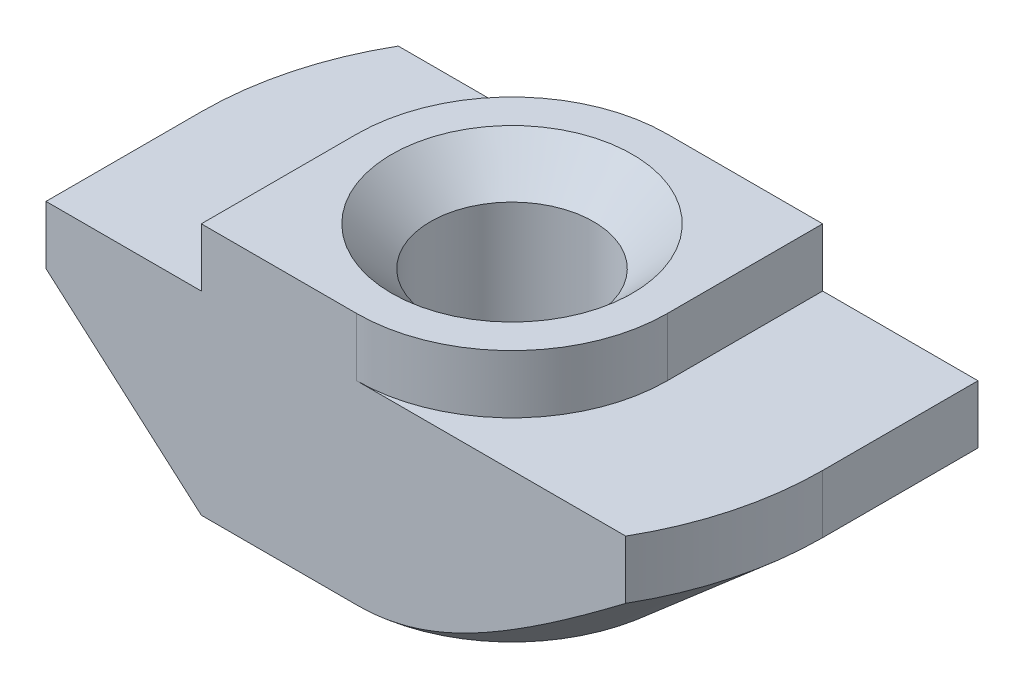
SolidWorks part; units mm, degrees
material "Сталь 20  ГОСТ 1050-2013"
ref_plane "Спереди" through (0, 0, 0) normal (0, 0, 1) x (1, 0, 0)
ref_plane "Сверху" through (0, 0, 0) normal (0, 1, 0) x (1, 0, 0)
ref_plane "Справа" through (0, 0, 0) normal (1, 0, 0) x (0, 0, -1)
sketch "Эскиз1" plane through (0, 0, 0) normal (0, 0, 1) x (1, 0, 0)
  line L0 (4, 0) -> (-4, 0)
  line L1 (-4, 0) -> (-4, -1.5)
  line L2 (-4, -1.5) -> (-8, -1.5)
  line L3 (-8, -1.5) -> (-8, -6.5)
  line L4 (-8, -6.5) -> (8, -6.5)
  line L5 (0, -6.5) -> (0, 0) construction
  line L6 (8, -1.5) -> (8, -6.5)
  line L7 (4, -1.5) -> (8, -1.5)
  line L8 (4, 0) -> (4, -1.5)
  dimension "D1" = 8
  dimension "D2" = 16
  dimension "D3" = 6.5
  dimension "D4" = 1.5
extrude "Бобышка-Вытянуть1" add sketch "Эскиз1" along normal mid plane 8
hole_wizard "Отверстие обработанное метчиком M52" positions "Эскиз2" profile "Эскиз3" tap size "M5" standard "ISO" end condition up to next
sketch "Эскиз2" plane through (0, 0, 0) normal (0, 1, 0) x (1, 0, 0)
  point P0 (0, 0)
sketch "Эскиз3" plane through (0, 0, 0) normal (1, 0, 0) x (0, 0, 1)
  line L0 (0, 0) -> (0, 6.5)
  line L1 (0, 6.5) -> (3.1, 6.5)
  line L2 (2.1, 5.5) -> (2.1, 1)
  line L3 (2.1, 1) -> (3.1, 0)
  line L5 (3.1, 0) -> (0, 0)
  line L6 (-2.1, 1) -> (-3.1, 0) construction
  line L7 (3.1, 6.5) -> (2.1, 5.5)
  line L8 (-3.1, 6.5) -> (-2.1, 5.5) construction
  line L11 (0, -6.35) -> (0, 107.95) construction
  dimension "Диаметр проходного сверла" = 4.2
  dimension "Глубина проходного сверла" = 6.5
  dimension "Диаметр передней зенковки" = 6.2
  dimension "Угол передней зенковки" = 90
  dimension "Диаметр задней зенковки" = 6.2
  dimension "Угол задней зенковки" = 90
cosmetic thread "Отверстие резьбы1" parameters "D2"=5
sketch "Эскиз4" plane through (0, 0, 0) normal (0, 1, 0) x (1, 0, 0)
  line L0 (-4, 4) -> (-4, 0)
  line L1 (-4, -4) -> (-4, 4) construction
  line L2 (4, 4) -> (-4, 4) construction
  line L3 (0, 4) -> (-4, 4)
  line L4 (0, -4) -> (4, -4)
  line L5 (4, -4) -> (-4, -4) construction
  line L6 (4, -4) -> (4, 0)
  line L7 (4, -4) -> (4, 4) construction
  arc A0 (-4, 0) -> (0, 4) centre (0, 0) cw
  arc A1 (4, 0) -> (0, -4) centre (0, 0) cw
extrude "Вырез-Вытянуть1" cut sketch "Эскиз4" against normal up to surface (1.5 mm away) up to face at (-6, -1.5, 0)
sketch "Эскиз5" plane through (0, -1.5, 0) normal (0, 1, 0) x (1, 0, 0)
  line L0 (-8, 0) -> (-8, 4)
  line L1 (-8, -4) -> (-8, 4) construction
  line L2 (-8, 4) -> (-6.9282, 4)
  line L3 (0, 4) -> (-8, 4) construction
  line L4 (8, 0) -> (8, -4)
  line L5 (8, -4) -> (8, 4) construction
  line L6 (8, -4) -> (6.9282, -4)
  line L7 (8, -4) -> (0, -4) construction
  arc A0 (-6.9282, 4) -> (-8, 0) centre (0, 0) ccw
  arc A2 (8, 0) -> (6.9282, -4) centre (0, 0) cw
  point P19 (0, 0)
extrude "Вырез-Вытянуть2" cut sketch "Эскиз5" against normal through all
sketch "Эскиз6" plane through (0, 0, 4) normal (0, 0, 1) x (1, 0, 0)
  line L0 (-8, -3) -> (-8, -6.5)
  line L1 (-8, -1.5) -> (-8, -6.5) construction
  line L2 (-8, -6.5) -> (-4, -6.5)
  line L3 (-8, -6.5) -> (6.9282, -6.5) construction
  line L4 (-4, -6.5) -> (-8, -3)
  line L5 (-4, -1.5) -> (-8, -1.5) construction
  line L6 (-4, 0) -> (-4, -1.5) construction
  point P10 (0, 0)
  dimension "D1" = 1.5
sketch "Эскиз7" plane through (0, -6.5, 0) normal (0, -1, 0) x (1, 0, 0)
  line L0 (0, 8) -> (-8, 8)
  line L1 (-8, 8) -> (-8, 0)
  line L2 (0, -8) -> (8, -8)
  line L3 (8, -8) -> (8, 0)
  arc A0 (-8, 0) -> (0, -8) centre (0, 0) ccw
  arc A1 (8, 0) -> (0, 8) centre (0, 0) ccw
sweep "Вырез-По траектории1" cut profiles "Эскиз6" path "Эскиз7"
